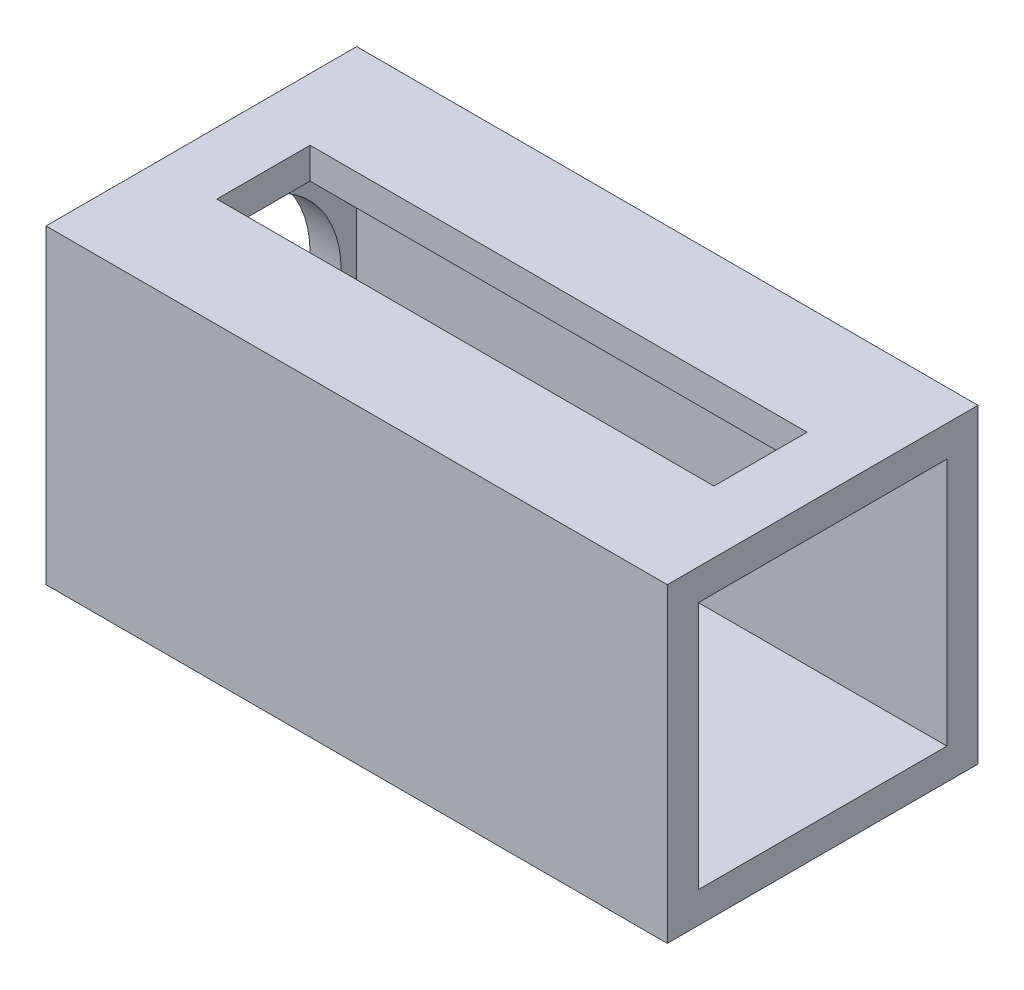
SolidWorks part; units mm, degrees
ref_plane "Front Plane" through (0, 0, 0) normal (0, 0, 1) x (1, 0, 0)
ref_plane "Top Plane" through (0, 0, 0) normal (0, 1, 0) x (1, 0, 0)
ref_plane "Right Plane" through (0, 0, 0) normal (1, 0, 0) x (0, 0, -1)
sketch "Sketch1" plane through (0, 0, 0) normal (0, 0, 1) x (1, 0, 0)
  line L1 (-10, -5) -> (10, -5)
  line L2 (-10, -5) -> (-10, 5)
  line L3 (-10, 5) -> (10, 5)
  line L4 (10, -5) -> (10, 5)
  line L5 (-10, -5) -> (10, 5) construction
  line L6 (-10, 5) -> (10, -5) construction
  point P0 (0, 0)
  dimension "D1" = 10
  dimension "D2" = 20
extrude "Boss-Extrude1" add sketch "Sketch1" along normal blind 10
ref_plane "Plane1" through (0, 0, -20) normal (0, 0, 1) x (1, 0, 0)
shell "Shell1" thickness 1
sketch "Sketch3" plane through (-10, 0, 0) normal (-1, 0, 0) x (0, 0, 1)
  circle A0 centre (5, 0) radius 3.5
  dimension "D1" = 7
  dimension "D2" = 5
extrude "Cut-Extrude1" cut sketch "Sketch3" against normal up to next
sketch "Sketch5" plane through (0, 5, 0) normal (0, 1, 0) x (1, 0, 0)
  line L0 (-10, -10) -> (-10, 0) construction
  line L1 (8, -6.5) -> (-8, -6.5)
  line L2 (8, -6.5) -> (8, -3.5)
  line L3 (8, -3.5) -> (-8, -3.5)
  line L4 (-8, -6.5) -> (-8, -3.5)
  line L5 (8, -6.5) -> (-8, -3.5) construction
  line L6 (8, -3.5) -> (-8, -6.5) construction
  line L7 (10, -10) -> (-10, -10) construction
  point P0 (0, -5)
  dimension "D1" = 16
  dimension "D2" = 3
  dimension "D3" = 2
  dimension "D4" = 5
extrude "Cut-Extrude2" cut sketch "Sketch5" against normal up to next
